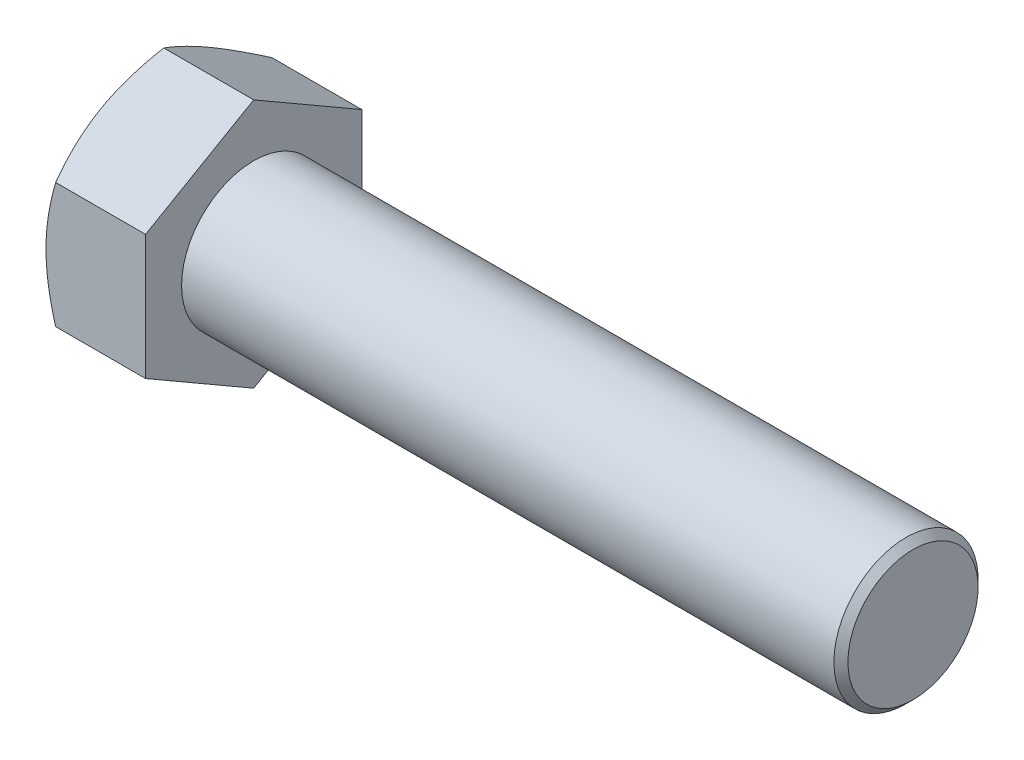
SolidWorks part; units mm, degrees
extrude "BaseHead" add sketch "Sketch1" along normal blind 15.3416
sketch "Sketch1" plane through (0, 0, 0) normal (1, 0, 0) x (0, 0, -1)
  line L0 (16.6624, 9.62) -> (16.6624, -9.62)
  line L1 (-16.6624, 9.62) -> (-16.6624, -9.62)
  line L2 (16.6624, -9.62) -> (0, -19.2401)
  line L3 (0, -19.2401) -> (-16.6624, -9.62)
  line L4 (16.6624, 9.62) -> (0, 19.2401)
  line L5 (0, 19.2401) -> (-16.6624, 9.62)
  dimension "Width_flats" = 33.3248
  dimension "D2" = 120
  dimension "D3" = 16.6624
  dimension "D4" = 16.6624
  dimension "D5" = 16.6624
material "AISI Type 316L stainless steel"
ref_plane "Plane1" through (0, 0, 0) normal (0, 0, 1) x (1, 0, 0)
ref_plane "Plane2" through (0, 0, 0) normal (0, 1, 0) x (1, 0, 0)
ref_plane "Plane3" through (0, 0, 0) normal (1, 0, 0) x (0, 0, -1)
sketch "BodySke" plane through (0, 0, 0) normal (0, 0, 1) x (1, 0, 0)
  line L0 (0, 9.62) -> (0, -9.62) construction
  line L1 (0, 0) -> (116.9416, 0)
  line L2 (0, 0) -> (0, 11.1125)
  line L3 (0, 11.1125) -> (115.8621, 11.1125)
  line L4 (116.9416, 0) -> (116.9416, 10.033)
  line L5 (15.3416, 19.2401) -> (15.3416, 9.62) construction
  line L6 (116.9416, 10.033) -> (115.8621, 11.1125)
  line L7 (0, 0) -> (96.52, 0) construction
  line L8 (116.9416, -10.033) -> (115.8621, -11.1125) construction
  line L9 (0, -11.1125) -> (115.8621, -11.1125) construction
  line L10 (17.1552, 15.24) -> (17.1552, -2.54) construction
  line L11 (66.1416, 15.24) -> (66.1416, -2.54) construction
  line L12 (15.3416, 9.62) -> (15.3416, -9.62) construction
  dimension "Diameter" = 22.225
revolve "BaseBody" add sketch "BodySke" angle 360 about L7
cosmetic thread "ThreadCosmetic" parameters "Thread_length"=50.8, "Thread_minor"=20.066
sketch "Sketch3" plane through (0, 0, 0) normal (0, 0, 1) x (1, 0, 0)
  line L0 (0, 16.6624) -> (5.1544, 25.5901)
  line L1 (0, 19.2401) -> (0, 9.62) construction
  line L2 (5.1544, 25.5901) -> (5.1544, 31.9401)
  line L3 (5.1544, 31.9401) -> (-12.7, 31.9401)
  line L4 (-12.7, 31.9401) -> (-12.7, 16.6624)
  line L5 (-12.7, 16.6624) -> (0, 16.6624)
  line L6 (0, 0) -> (99.06, 0) construction
  line L7 (15.3416, 19.2401) -> (0, 19.2401) construction
  dimension "D1" = 16.6624
  dimension "D2" = 6.35
  dimension "D3" = 12.7
  dimension "D4" = 6.35
  dimension "Head_ch_ang" = 30
revolve "HeadChamfer" cut sketch "Sketch3" angle 360 about L6
fillet "HeadFillet" [suppressed] radius 1.524
sketch "ThdSchSke" plane through (0, 0, 0) normal (0, 0, 1) x (1, 0, 0)
  line L0 (66.1416, -10.033) -> (65.3857, -11.1125)
  line L1 (66.1416, -10.033) -> (66.8975, -11.1125)
  line L2 (66.8975, -11.1125) -> (66.8975, -13.8906)
  line L3 (-3.175, 0) -> (5.1513, 0) construction
  line L5 (66.8975, -13.8906) -> (65.3857, -13.8906)
  line L6 (65.3857, -13.8906) -> (65.3857, -11.1125)
  dimension "Diameter" = 22.225
revolve "ThreadSchematic" [suppressed] cut sketch "ThdSchSke" angle 360 about L3
pattern_linear "ThdSchPat" [suppressed]
equation "\"D3@Sketch1\" = \"Width_flats@Sketch1\" / 2"
equation "\"D4@Sketch1\" = \"D3@Sketch1\""
equation "\"D5@Sketch1\" = \"D4@Sketch1\""
equation "\"Thread_minor@ThreadCosmetic\" = \"Minor_dia@BodySke\""
equation "\"D1@Sketch3\" = \"Width_flats@Sketch1\" / 2"
equation "\"Thread_length@ThreadCosmetic\" = ((sgn( (\"Length@BodySke\" - \"Advance@BodySke\" ) - \"Thread_nom@BodySke\" )-1)*( (\"Length@BodySke\" - \"Advance@BodySke\" ) - \"Thread_nom@BodySke\" ))/-2+ \"Thread_nom@BodySke\""
equation "\"Thread_minor@ThdSchSke\" = \"Minor_dia@BodySke\""
equation "\"Diameter@ThdSchSke\" = \"Diameter@BodySke\""
equation "\"Overcut@ThdSchSke\" = \"Diameter@BodySke\" * 1.25"
equation "\"Start@ThdSchSke\" = \"Head_ht@BaseHead\" + \"Length@BodySke\" - \"Thread_length@ThreadCosmetic\"  '---Non-countersunk---"
equation "\"Num_threads@ThdSchPat\" = int( \"Thread_length@ThreadCosmetic\" / \"Advance@BodySke\" + 0.999 )  + 1"
equation "\"Advance@ThdSchPat\" = \"Thread_length@ThreadCosmetic\" /  (\"Num_threads@ThdSchPat\" - 1) 'relax it"
equation "\"Num_threads@ThdSchPat\" = \"Num_threads@ThdSchPat\" - sgn( \"Num_threads@ThdSchPat\" - 1) '---chamfered tips only---"
